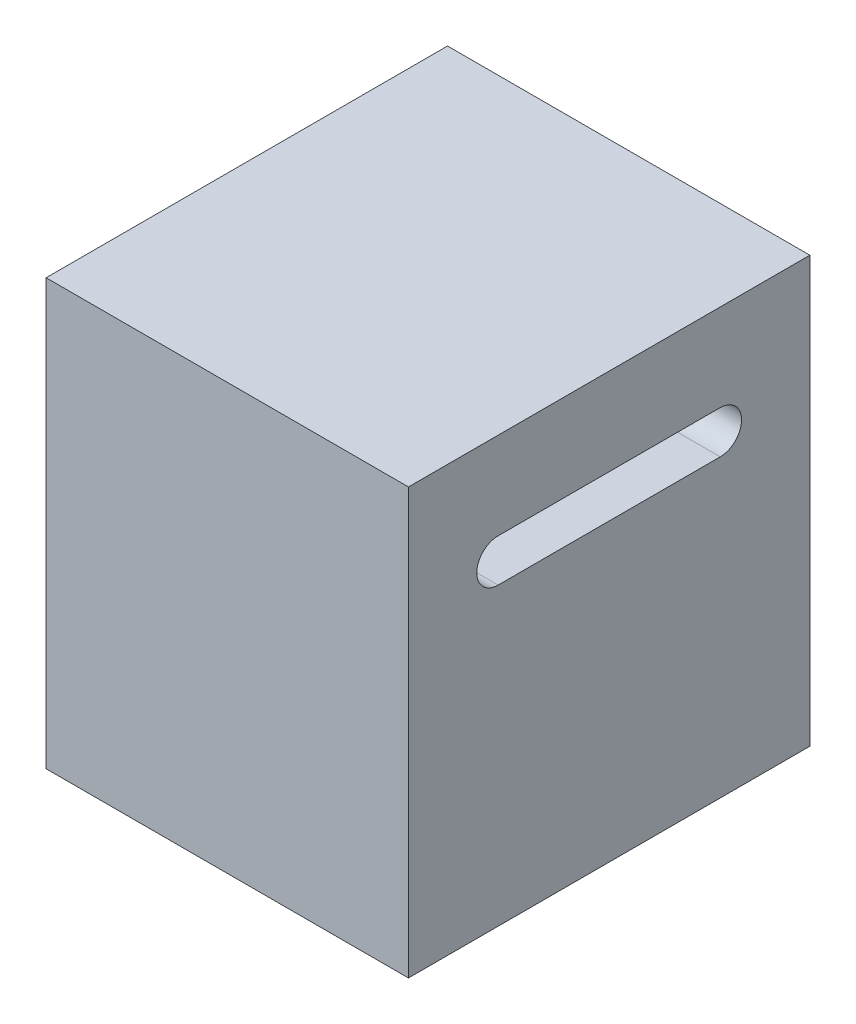
SolidWorks part; units mm, degrees
ref_plane "Front Plane" through (0, 0, 0) normal (0, 0, 1) x (1, 0, 0)
ref_plane "Top Plane" through (0, 0, 0) normal (0, 1, 0) x (1, 0, 0)
ref_plane "Right Plane" through (0, 0, 0) normal (1, 0, 0) x (0, 0, -1)
sketch "Sketch1" plane through (0, 0, 0) normal (0, 1, 0) x (1, 0, 0)
  line L1 (0, 0) -> (42.418, 0)
  line L2 (0, 0) -> (0, 46.99)
  line L3 (0, 46.99) -> (42.418, 46.99)
  line L4 (42.418, 0) -> (42.418, 46.99)
  dimension "D1" = 46.99
  dimension "D2" = 42.418
extrude "Boss-Extrude1" add sketch "Sketch1" along normal blind 49.784
sketch "Sketch2" plane through (42.418, 0, 0) normal (1, 0, 0) x (0, 0, -1)
  line L0 (10.495, 37.084) -> (36.495, 37.084) construction
  line L1 (10.495, 39.5801) -> (36.495, 39.5801)
  line L2 (10.495, 34.5879) -> (36.495, 34.5879)
  line L3 (0, 49.784) -> (46.99, 49.784) construction
  arc A0 (10.495, 39.5801) -> (10.495, 34.5879) centre (10.495, 37.084) ccw
  arc A1 (36.495, 34.5879) -> (36.495, 39.5801) centre (36.495, 37.084) ccw
  point P2 (23.495, 37.084)
  point P9 (23.495, 39.5801)
  point P10 (23.495, 49.784)
  dimension "D4" = 2.4961
  dimension "D1" = 12.7
  dimension "D2" = 26
extrude "Cut-Extrude1" cut sketch "Sketch2" against normal through all
